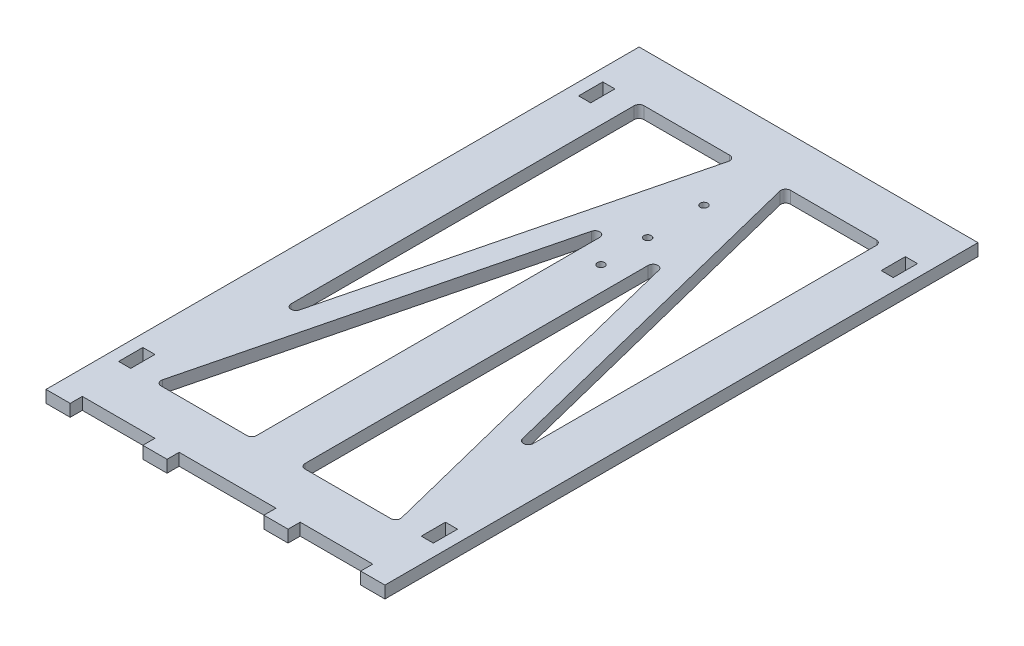
SolidWorks part; units mm, degrees
material "Beech"
ref_plane "Front Plane" through (0, 0, 0) normal (0, 0, 1) x (1, 0, 0)
ref_plane "Top Plane" through (0, 0, 0) normal (0, 1, 0) x (1, 0, 0)
ref_plane "Right Plane" through (0, 0, 0) normal (1, 0, 0) x (0, 0, -1)
sketch "Sketch1" plane through (0, 0, 0) normal (0, 1, 0) x (1, 0, 0)
  line L0 (0, 0) -> (177.8, 0)
  line L1 (0, 0) -> (0, 304.8)
  line L2 (177.8, 0) -> (177.8, 304.8)
  line L3 (0, 304.8) -> (177.8, 304.8)
  line L4 (0, 0) -> (12.7, 0)
  line L5 (0, 0) -> (0, -6.35)
  line L6 (12.7, 0) -> (12.7, -6.35)
  line L7 (0, -6.35) -> (12.7, -6.35)
  line L8 (50.8, 0) -> (63.5, 0)
  line L9 (50.8, 0) -> (50.8, -6.35)
  line L10 (63.5, 0) -> (63.5, -6.35)
  line L11 (50.8, -6.35) -> (63.5, -6.35)
  line L12 (114.3, 0) -> (127, 0)
  line L13 (114.3, 0) -> (114.3, -6.35)
  line L14 (127, 0) -> (127, -6.35)
  line L15 (114.3, -6.35) -> (127, -6.35)
  line L16 (177.8, 0) -> (165.1, 0)
  line L17 (177.8, 0) -> (177.8, -6.35)
  line L18 (165.1, 0) -> (165.1, -6.35)
  line L19 (177.8, -6.35) -> (165.1, -6.35)
  line L20 (165.1, 279.4) -> (171.45, 279.4)
  line L21 (165.1, 279.4) -> (165.1, 266.7)
  line L22 (171.45, 279.4) -> (171.45, 266.7)
  line L23 (165.1, 266.7) -> (171.45, 266.7)
  line L24 (6.35, 279.4) -> (12.7, 279.4)
  line L25 (6.35, 279.4) -> (6.35, 266.7)
  line L26 (12.7, 279.4) -> (12.7, 266.7)
  line L27 (6.35, 266.7) -> (12.7, 266.7)
  line L28 (6.35, 38.1) -> (12.7, 38.1)
  line L29 (6.35, 38.1) -> (6.35, 25.4)
  line L30 (12.7, 38.1) -> (12.7, 25.4)
  line L31 (6.35, 25.4) -> (12.7, 25.4)
  line L32 (171.45, 38.1) -> (165.1, 38.1)
  line L33 (171.45, 38.1) -> (171.45, 25.4)
  line L34 (165.1, 38.1) -> (165.1, 25.4)
  line L35 (171.45, 25.4) -> (165.1, 25.4)
  line L36 (76.2, 279.4) -> (25.4, 279.4)
  line L37 (25.4, 279.4) -> (25.4, 76.2)
  line L38 (25.4, 76.2) -> (76.2, 279.4)
  line L39 (101.6, 279.4) -> (152.4, 279.4)
  line L40 (152.4, 279.4) -> (152.4, 76.2)
  line L41 (152.4, 76.2) -> (101.6, 279.4)
  line L42 (76.2, 228.6) -> (76.2, 25.4)
  line L43 (76.2, 25.4) -> (25.4, 25.4)
  line L44 (25.4, 25.4) -> (76.2, 228.6)
  line L45 (101.6, 228.6) -> (101.6, 25.4)
  line L46 (101.6, 25.4) -> (152.4, 25.4)
  line L47 (152.4, 25.4) -> (101.6, 228.6)
  circle A1 centre (88.9, 249.9) radius 1.935
  circle A2 centre (88.9, 220.4) radius 1.935
  circle A3 centre (88.9, 195.9) radius 1.935
  point P21 (88.9, 304.8)
  dimension "D8" = 12.7
  dimension "D6" = 3.87
  dimension "D1" = 177.8
  dimension "D2" = 304.8
  dimension "D3" = 29.5
  dimension "D4" = 54.9
  dimension "D5" = 24.5
  dimension "D7" = 6.35
  dimension "D9" = 25.4
  dimension "D10" = 50.8
  dimension "D11" = 50.8
  dimension "D12" = 12.7
  dimension "D13" = 25.4
  dimension "D14" = 6.35
  dimension "D15" = 6.35
  dimension "D16" = 12.7
  dimension "D17" = 203.2
  dimension "D18" = 50.8
  dimension "D19" = 50.8
  dimension "D20" = 12.7
extrude "Front Panel" add sketch "Sketch1" along normal blind 6.35
fillet "Fillet1" radius 2.54 12 edges at (25.4, 3.175, -279.4) (76.2, 3.175, -279.4) (25.4, 3.175, -76.2) (25.4, 3.175, -25.4) (76.2, 3.175, -25.4) (76.2, 3.175, -228.6) (101.6, 3.175, -228.6) (101.6, 3.175, -25.4) (152.4, 3.175, -25.4) (152.4, 3.175, -76.2) (152.4, 3.175, -279.4) (101.6, 3.175, -279.4)
equation "\"CageLeftBottomEdge\"=22.11mm"
equation "\"CageLeftTopEdge\"=22.11mm"
equation "\"CageRightBottomEdge\"=21.63mm"
equation "\"CageRightTopEdge\"=21.63mm"
equation "\"CageHeight\"=86.04mm"
equation "\"CageLength\"=73.76mm"
equation "\"CageTopScrewClearance\"=10mm"
equation "\"CageBottomScrewClearance\"=25mm"
equation "\"CageLeftTopDepth\"= 11.65mm"
equation "\"CageLeftBottomDepth\"=11.11mm"
equation "\"CageLeftTopHeight\"=8.56175mm"
equation "\"CageLeftBottomHeight\"=16mm"
equation "\"CageRightTopDepth\"= 11.05mm"
equation "\"CageRightBottomDepth\"=10.58mm"
equation "\"CageRightTopHeight\"=9.6mm"
equation "\"CageRightBottomHeight\"=15.49mm"
equation "\"CageLeftTopChannelDepth\"=2.41908mm"
equation "\"CageLeftBottomChannelDepth\"=2.588mm"
equation "\"CageLeftChannelHeight\"=11.7mm"
equation "\"CageRightTopChannelDepth\"=2.32mm"
equation "\"CageRightBottomChannelDepth\"=2.318mm"
equation "\"CageRightChannelHeight\"=10mm"
equation "\"CageChanRelHeight\"=23.99mm"
equation "\"CageChanRelDepth\"=5.492mm"
equation "\"CageChamberRadius\"=16.261mm"
equation "\"CageScrewDiameter\"=4.8mm"
equation "\"CageSetScrewDiameter\"=3.5mm"
equation "\"CageAxleRadius\"=6.639mm"
equation "\"CageAxleKeyHeight\"=1.619mm"
equation "\"CageAxleKeyWidth\"=2.662mm"
equation "\"CageHoseWindowWidth\"=16.29mm"
equation "\"CageHoseWindowHeight\"=26.5mm"
equation "\"CageHoseWindow-Edge\"=8.89mm"
equation "\"CageScrew-VerticalEdge\"=5.0mm"
equation "\"CageScrew-HorizontalEdge\"=7.5mm"
equation "\"CageScrew-HoseCornerScrewEdge\"=4.45mm"
equation "\"CageAxle-BottomEdge\"=56.05mm"
equation "\"CageAxle-FrontEdge\"=46.03mm"
equation "\"CageBackSetScrew-Axle\"=40mm"
equation "\"CageFrontSetScrew-Axle\"=22mm"
equation "\"CageVelocityWindow-BackEdge\"=34.8mm"
equation "\"CageVelocityWindow-BottomEdge\"=27.55mm"
equation "\"CageVelocityWindowHeight\"=22.29mm"
equation "\"CageVelocityWindowWidth\"=12.61mm"
equation "\"TriggerSlot-BottomEdge\"=6.35mm"
equation "\"TriggerSlot-FrontEdge\"=15mm"
equation "\"TriggerSlotSize\"=6.7mm"
equation "\"TriggerRackOffset\"=6mm"
equation "\"TriggerSlotSizeInt\"=.25in"
equation "\"MotorMountLegLength\"=.25in"
equation "\"GearOffset\"=.264907in"
equation "\"TriggerSlotSpacing\"=.25in"
equation "\"TriggerMiniSlotWidth\"=3.5mm"
equation "\"TriggerRackWidth\"=6.5mm"
equation "\"pandiscradius\"=14in"
equation "\"towermaterialwidth\"=.25in"
equation "\"towerslotlength\"=.5in"
equation "\"towermarkerspace\"=5in"
equation "\"towerslothorizoffset\"=1in"
equation "\"towerslothorizspacing\"=2in"
equation "\"towerslotvertoffset\"=3in"
equation "\"towerslotvertspacing\"=1in"
equation "\"towerheight\"=12in"
equation "\"towerupslot\"=1in"
equation "\"D1@Sketch1\"=(\"towerslothorizoffset\"+\"towerslothorizspacing\"+\"towerslotlength\")*2"
equation "\"D2@Sketch1\"=\"towerheight\""
equation "\"D3@Sketch1\"=\"ajax4020gap\""
equation "\"D4@Sketch1\"=\"ajax4020gap\"+1in"
equation "\"D5@Sketch1\"=\"ajax4010gap\""
equation "\"D6@Sketch1\"=\"ajaxaxlesize\""
equation "\"D7@Sketch1\"=\"towermaterialwidth\""
equation "\"toweraxle\"=.5in"
equation "\"D8@Sketch1\"=\"towerslotlength\""
equation "\"D9@Sketch1\"=\"towerupslot\""
equation "\"D10@Sketch1\"=\"towerslothorizspacing\""
equation "\"D11@Sketch1\"=\"towerslothorizspacing\""
equation "\"D12@Sketch1\"=\"towerslotlength\""
equation "\"D13@Sketch1\"=\"towerupslot\""
equation "\"D1@Front Panel\"=\"towermaterialwidth\""
equation "\"stepperouterrad\"=10mm"
equation "\"stepperscrewsize\"=3.45mm"
equation "\"stepperscrewc2c\"=49.5mm"
equation "\"stepperdepthoffset\"=24mm"
equation "\"stepperhorizoffset\"=22.91mm"
equation "\"shaftslotOD\"=18.8mm"
equation "\"shaftslotID\"=13.28mm"
equation "\"shaftkeywidth\"=2.67mm"
equation "\"shaftkeydepth\"=1.8mm"
equation "\"shaftcollartotaldepth\"=12.5mm"
equation "\"shaftsquaredepth\"=6mm"
equation "\"shaftsetscrewsize\"=3.5mm"
equation "\"shaftkeytightdepth\"=1.85mm"
equation "\"shaftslottightID\"=12.78mm"
equation "\"shaftsetscrewoffset\"=9mm"
equation "\"cagecollartotaldepth\"=10mm"
equation "\"cagecollartotalwidth\"=35mm"
equation "\"cagecollarbasedepth\"=4mm"
equation "\"ajaxaxlesize\"=3.87mm"
equation "\"ajax4020gap\"=29.5mm"
equation "\"ajax4010gap\"=24.5mm"
equation "\"D14@Sketch1\"=\"towermaterialwidth\""
equation "\"D15@Sketch1\"=\"towermaterialwidth\""
equation "\"D16@Sketch1\"=\"toweraxle\""
equation "\"towerspeedwidth\"=2in"
equation "\"towerspeedheight\"=8in"
equation "\"towerspeedgap\"=2in"
equation "\"stepperaxleflat\"=.037in"
equation "\"stepperaxlerad\"=0.11811024in"
equation "\"ajaxinnercut\"=2.3mm"
equation "\"ajaxwidth\"=6.1mm"
equation "\"ajaxdiametral\"=25.8854"
equation "\"ajaxcutoutdepth\"=2.3mm"
equation "\"ajax20hubbuffer\"=6.1mm"
equation "\"ajax20hubholeoffset\"=.19685in"
equation "\"ajax20hubholesize\"=.059055in"
equation "\"ajax20cutoutint\"=13.4mm"
equation "\"ajax40hubholesize\"=7.21mm"
equation "\"ajax40hubholeoffset\"=10mm"
equation "\"ajax40hubbuffer\"=8.9mm"
equation "\"ajax40cutoutint\"=32.6mm"
equation "\"bearingpandiscrad\"=6.8in"
equation "\"bearingpandiscang\"=48.75deg"
equation "\"bearingclearholedist\"=4.7345in"
equation "\"bearingclearholesize\"=.5in"
equation "\"bearingclearholeang\"=22.5deg"
equation "\"bearingmountholedist\"=4.25in"
equation "\"bearingwirehole\"=1.5in"
equation "\"no6diam\"=.146in"
equation "\"D17@Sketch1\"=\"towerspeedheight\""
equation "\"D19@Sketch1\"=\"towerspeedgap\""
equation "\"D18@Sketch1\"=\"towerspeedwidth\""
equation "\"D20@Sketch1\"=\"toweraxle\""
equation "\"gearhubintdiam\"=30mm"
equation "\"gearhubintwid\"=15mm"
equation "\"shortconangle\"=20deg"
equation "\"shortconlen\"=.875in"
equation "\"longconlen\"=1.25in"
equation "\"longconangle\"=15deg"
